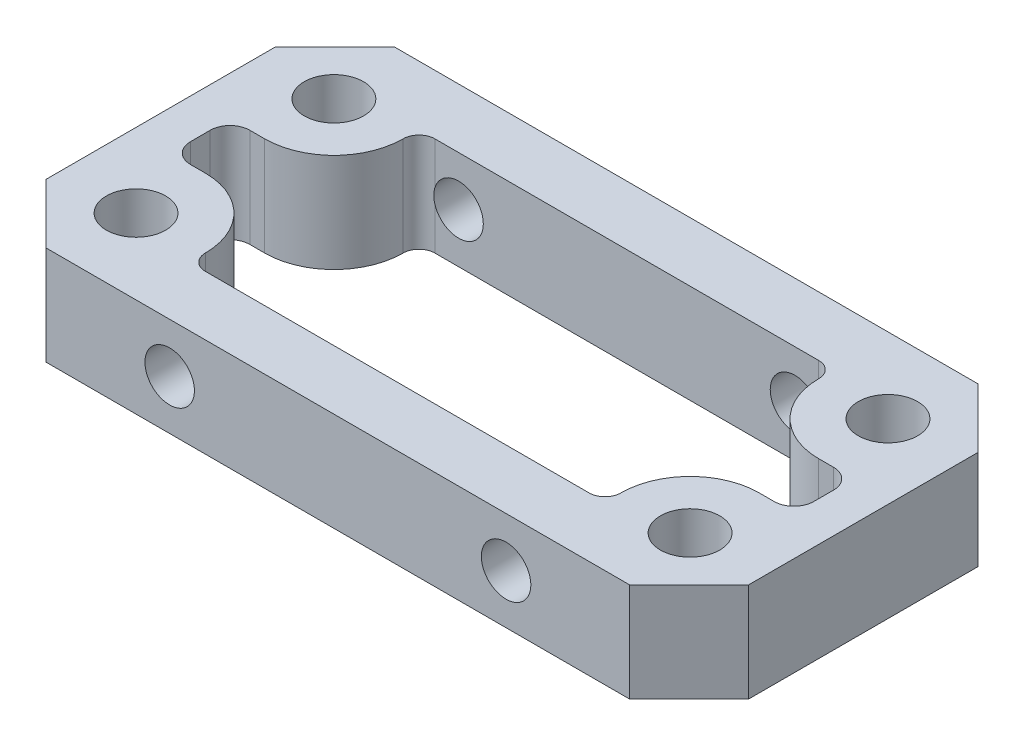
SolidWorks part; units mm, degrees
material "6061-T6 (SS)"
ref_plane "前视基准面" through (0, 0, 0) normal (0, 0, 1) x (1, 0, 0)
ref_plane "上视基准面" through (0, 0, 0) normal (0, 1, 0) x (1, 0, 0)
ref_plane "右视基准面" through (0, 0, 0) normal (1, 0, 0) x (0, 0, -1)
sketch "草图1" plane through (0, 0, 0) normal (0, 1, 0) x (1, 0, 0)
  line L2 (-17.75, 8.8) -> (17.75, 8.8)
  line L3 (-17.75, 8.8) -> (-17.75, -8.8)
  line L4 (-17.75, -8.8) -> (17.75, -8.8)
  line L5 (17.75, 8.8) -> (17.75, -8.8)
  line L6 (0, -8.8) -> (0, 8.8) construction
  line L7 (-17.75, 0) -> (17.75, 0) construction
  line L8 (-14, 5) -> (14, 5) construction
  line L9 (-14, 5) -> (-14, -5) construction
  line L10 (-14, -5) -> (14, -5) construction
  line L11 (14, 5) -> (14, -5) construction
  line L12 (0, -5) -> (0, 5) construction
  line L13 (-14, 0) -> (14, 0) construction
  circle A0 centre (-14, 5) radius 1.5
  circle A1 centre (-14, -5) radius 1.5
  circle A2 centre (14, -5) radius 1.5
  circle A3 centre (14, 5) radius 1.5
  point P0 (0, 0)
  point P2 (0, 0)
  dimension "D5" = 3
  dimension "D1" = 17.6
  dimension "D2" = 35.5
  dimension "D3" = 10
  dimension "D4" = 28
extrude "凸台-拉伸1" add sketch "草图1" along normal blind 38
cosmetic thread "装饰螺纹线13" parameters "D2"=4
cosmetic thread "装饰螺纹线14" parameters "D2"=4
cosmetic thread "装饰螺纹线15" parameters "D2"=4
cosmetic thread "装饰螺纹线16" parameters "D2"=4
sketch "草图2" plane through (0, 38, 0) normal (0, 1, 0) x (1, 0, 0)
  line L0 (0, 0) -> (0, -50000) construction
  line L1 (0, 0) -> (-50000, 0) construction
  line L2 (9.7, 5.8) -> (-9.7, 5.8)
  line L5 (17.75, 8.8) -> (-17.75, 8.8) construction
  line L6 (-14, 1.5) -> (-14.75, 1.5)
  line L7 (-15.75, 0.5) -> (-15.75, -0.5)
  line L8 (-17.75, 8.8) -> (-17.75, -8.8) construction
  line L9 (9.7, -5.8) -> (-9.7, -5.8)
  line L10 (-14, -1.5) -> (-14.75, -1.5)
  line L11 (14, -1.5) -> (14.75, -1.5)
  line L12 (15.75, 0.5) -> (15.75, -0.5)
  line L13 (14, 1.5) -> (14.75, 1.5)
  arc A0 (-9.7, 5.8) -> (-10.5, 5) centre (-9.7, 5) ccw
  arc A1 (-10.5, 5) -> (-14, 1.5) centre (-14, 5) cw
  arc A2 (-14.75, 1.5) -> (-15.75, 0.5) centre (-14.75, 0.5) ccw
  circle A3 centre (-14, 5) radius 1.5 construction
  circle A4 centre (-14, 5) radius 1.5 construction
  arc A5 (-9.7, -5.8) -> (-10.5, -5) centre (-9.7, -5) cw
  arc A6 (-10.5, -5) -> (-14, -1.5) centre (-14, -5) ccw
  arc A7 (-14.75, -1.5) -> (-15.75, -0.5) centre (-14.75, -0.5) cw
  arc A8 (9.7, -5.8) -> (10.5, -5) centre (9.7, -5) ccw
  arc A9 (10.5, -5) -> (14, -1.5) centre (14, -5) cw
  arc A10 (14.75, -1.5) -> (15.75, -0.5) centre (14.75, -0.5) ccw
  arc A11 (14.75, 1.5) -> (15.75, 0.5) centre (14.75, 0.5) cw
  arc A12 (10.5, 5) -> (14, 1.5) centre (14, 5) ccw
  arc A13 (9.7, 5.8) -> (10.5, 5) centre (9.7, 5) cw
  point P30 (-15.75, 0)
  point P33 (0, -5.8)
  point P46 (0, 5.8)
  dimension "D2" = 3.5
  dimension "1" = 1
  dimension "D1" = 3
  dimension "D3" = 2
extrude "切除-拉伸1" cut sketch "草图2" against normal through all
sketch "草图4" plane through (0, 0, 8.8) normal (0, 0, 1) x (1, 0, 0)
  line L0 (17.75, 0) -> (-17.75, 38) construction
  line L3 (-17.75, 0) -> (17.75, 0) construction
  line L4 (-17.75, 38) -> (-17.75, 0) construction
  line L5 (-14.75, 33) -> (14.75, 33)
  line L6 (-14.75, 33) -> (-14.75, 5)
  line L7 (-14.75, 5) -> (14.75, 5)
  line L8 (14.75, 33) -> (14.75, 5)
  line L9 (0, 5) -> (0, 33) construction
  line L10 (-14.75, 19) -> (14.75, 19) construction
  point P3 (0, 19)
  dimension "D1" = 5
  dimension "D2" = 3
extrude "切除-拉伸3" cut sketch "草图4" against normal through all
sketch "草图5" plane through (0, 0, 8.8) normal (0, 0, 1) x (1, 0, 0)
  line L0 (-17.75, 38) -> (-17.75, 0) construction
  line L1 (-17.75, 33) -> (17.75, 33)
  line L2 (-17.75, 33) -> (-17.75, 0)
  line L3 (-17.75, 0) -> (17.75, 0)
  line L4 (17.75, 33) -> (17.75, 0)
  line L5 (0, 0) -> (0, 33) construction
  line L6 (-17.75, 16.5) -> (17.75, 16.5) construction
  line L7 (17.75, 38) -> (17.75, 0) construction
  line L8 (-17.75, 0) -> (17.75, 0) construction
  line L9 (14.75, 33) -> (-14.75, 33) construction
  line L10 (14.75, 33) -> (-14.75, 33) construction
  point P392 (0, 16.5)
extrude "切除-拉伸4" cut sketch "草图5" against normal through all
chamfer "倒角1" distance 3 angle 45 4 edges at (-17.75, 35.5, -8.8) (17.75, 35.5, -8.8) (17.75, 35.5, 8.8) (-17.75, 35.5, 8.8)
sketch "草图6" plane through (0, 0, -8.8) normal (0, 0, -1) x (-1, 0, 0)
  line L0 (0, 38) -> (0, -49962) construction
  line L1 (-14.75, 38) -> (14.75, 38) construction
  point P4 (0, 38)
sketch "草图7" plane through (0, 0, -8.8) normal (0, 0, -1) x (-1, 0, 0)
  line L0 (-9.7, 38) -> (9.7, 38) construction
  line L1 (-9.7, 38) -> (9.7, 38) construction
  line L2 (-14.75, 35.5) -> (49985.25, 35.5) construction
  line L3 (-14.75, 38) -> (-14.75, 33) construction
  line L4 (0, 200038) -> (0, -249962) construction
  line L5 (0, 38) -> (0, -46776.482) construction
  circle A0 centre (-8.5, 35.5) radius 1.25
  circle A1 centre (8.5, 35.5) radius 1.25
  point P6 (-14.75, 35.5)
  point P13 (0, 38)
  dimension "D1" = 2.5
  dimension "D2" = 8.5
extrude "切除-拉伸5" cut sketch "草图7" against normal through all
cosmetic thread "装饰螺纹线9" parameters "D2"=3
cosmetic thread "装饰螺纹线10" parameters "D2"=3
cosmetic thread "装饰螺纹线11" parameters "D2"=3
cosmetic thread "装饰螺纹线12" parameters "D2"=3
